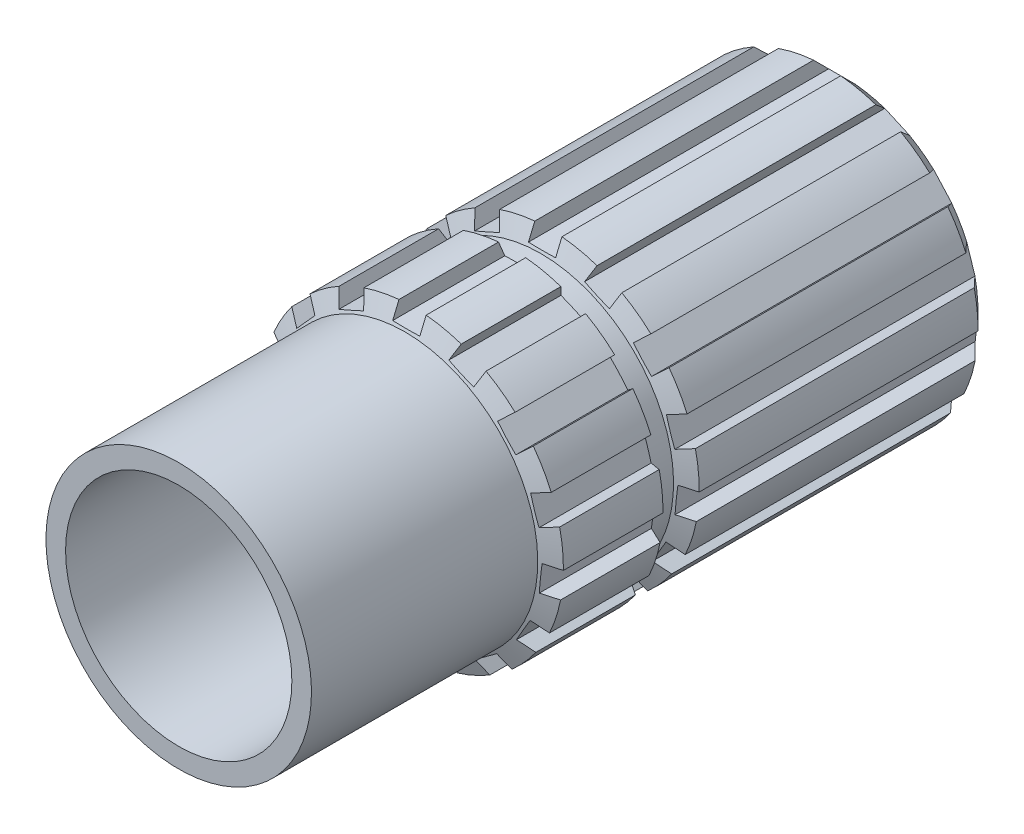
SolidWorks part; units mm, degrees
ref_plane "Front Plane" through (0, 0, 0) normal (0, 0, 1) x (1, 0, 0)
ref_plane "Top Plane" through (0, 0, 0) normal (0, 1, 0) x (1, 0, 0)
ref_plane "Right Plane" through (0, 0, 0) normal (1, 0, 0) x (0, 0, -1)
sketch "Sketch2" plane through (0, 0, 0) normal (1, 0, 0) x (0, 0, -1)
  line L0 (0, 0) -> (-103.5514, 0) construction
  line L1 (-27.9286, 9.525) -> (27.9286, 9.525)
  line L2 (27.9286, 9.525) -> (27.9286, 12.7)
  line L3 (-27.9286, 11.176) -> (-8.8786, 11.176)
  line L4 (-27.9286, 11.176) -> (-27.9286, 9.525)
  line L5 (-8.8786, 11.176) -> (-8.2436, 12.7)
  line L6 (-8.2436, 12.7) -> (0.1384, 12.7)
  line L7 (0.1384, 12.7) -> (0.7734, 11.176)
  line L8 (0.7734, 11.176) -> (2.5514, 11.176)
  line L9 (2.5514, 11.176) -> (3.1864, 12.7)
  line L10 (3.1864, 12.7) -> (27.9286, 12.7)
  point P5 (0, 9.525)
  dimension "D1" = 9.525
  dimension "D2" = 12.7
  dimension "D3" = 55.8571
  dimension "D4" = 1.651
  dimension "D5" = 0.635
  dimension "D6" = 0.635
  dimension "D7" = 0.635
  dimension "D8" = 19.05
  dimension "D9" = 1.778
  dimension "D10" = 9.652
revolve "Revolve1" add sketch "Sketch2" angle 360 about L0
chamfer "Chamfer1" distance 1.27 angle 45 1 edges at (0, 12.7, -27.9286)
sketch "Sketch3" plane through (0, 0, -27.9286) normal (0, 0, -1) x (-1, 0, 0)
  line L0 (0, 0.1797) -> (0, 13.5361) construction
  line L1 (-1.143, 11.3785) -> (1.143, 11.3785)
  line L2 (1.143, 11.3785) -> (1.143, 12.6485)
  line L3 (-1.143, 11.3785) -> (-1.143, 12.6485)
  line L4 (3.5839, 10.8596) -> (4.1004, 12.0198)
  line L5 (3.5839, 10.8596) -> (5.6722, 9.9298)
  line L6 (5.6722, 9.9298) -> (6.1888, 11.09)
  line L7 (7.691, 8.4631) -> (8.6348, 9.3129)
  line L8 (7.691, 8.4631) -> (9.2207, 6.7643)
  line L9 (9.2207, 6.7643) -> (10.1645, 7.6141)
  line L10 (10.4684, 4.6032) -> (11.6762, 4.9956)
  line L11 (10.4684, 4.6032) -> (11.1748, 2.4291)
  line L12 (11.1748, 2.4291) -> (12.3826, 2.8215)
  line L13 (11.4356, -0.0526) -> (12.6986, -0.1854)
  line L14 (11.4356, -0.0526) -> (11.1967, -2.3261)
  line L15 (11.1967, -2.3261) -> (12.4597, -2.4589)
  line L16 (10.4255, -4.6994) -> (11.5254, -5.3344)
  line L17 (10.4255, -4.6994) -> (9.2825, -6.6791)
  line L18 (9.2825, -6.6791) -> (10.3824, -7.3141)
  line L19 (7.6128, -8.5335) -> (8.3593, -9.561)
  line L20 (7.6128, -8.5335) -> (5.7634, -9.8772)
  line L21 (5.7634, -9.8772) -> (6.5099, -10.9047)
  line L22 (3.4837, -10.8922) -> (3.7478, -12.1344)
  line L23 (3.4837, -10.8922) -> (1.2477, -11.3675)
  line L24 (1.2477, -11.3675) -> (1.5117, -12.6097)
  line L25 (-1.2477, -11.3675) -> (-1.5117, -12.6097)
  line L26 (-1.2477, -11.3675) -> (-3.4837, -10.8922)
  line L27 (-3.4837, -10.8922) -> (-3.7478, -12.1344)
  line L28 (-5.7634, -9.8772) -> (-6.5099, -10.9047)
  line L29 (-5.7634, -9.8772) -> (-7.6128, -8.5335)
  line L30 (-7.6128, -8.5335) -> (-8.3593, -9.561)
  line L31 (-9.2825, -6.6791) -> (-10.3824, -7.3141)
  line L32 (-9.2825, -6.6791) -> (-10.4255, -4.6994)
  line L33 (-10.4255, -4.6994) -> (-11.5254, -5.3344)
  line L34 (-11.1967, -2.3261) -> (-12.4597, -2.4589)
  line L35 (-11.1967, -2.3261) -> (-11.4356, -0.0526)
  line L36 (-11.4356, -0.0526) -> (-12.6986, -0.1854)
  line L37 (-11.1748, 2.4291) -> (-12.3826, 2.8215)
  line L38 (-11.1748, 2.4291) -> (-10.4684, 4.6032)
  line L39 (-10.4684, 4.6032) -> (-11.6762, 4.9956)
  line L40 (-9.2207, 6.7643) -> (-10.1645, 7.6141)
  line L41 (-9.2207, 6.7643) -> (-7.691, 8.4631)
  line L42 (-7.691, 8.4631) -> (-8.6348, 9.3129)
  line L43 (-5.6722, 9.9298) -> (-6.1888, 11.09)
  line L44 (-5.6722, 9.9298) -> (-3.5839, 10.8596)
  line L45 (-3.5839, 10.8596) -> (-4.1004, 12.0198)
  circle A0 centre (0, 0) radius 12.7 construction
  arc A1 (-10.1645, 7.6141) -> (-11.6762, 4.9956) centre (0, 0) ccw
  arc A2 (-6.1888, 11.09) -> (-8.6348, 9.3129) centre (0, 0) ccw
  arc A3 (-1.143, 12.6485) -> (-4.1004, 12.0198) centre (0, 0) ccw
  arc A4 (4.1004, 12.0198) -> (1.143, 12.6485) centre (0, 0) ccw
  arc A5 (8.6348, 9.3129) -> (6.1888, 11.09) centre (0, 0) ccw
  arc A6 (11.6762, 4.9956) -> (10.1645, 7.6141) centre (0, 0) ccw
  arc A7 (12.6986, -0.1854) -> (12.3826, 2.8215) centre (0, 0) ccw
  arc A8 (11.5254, -5.3344) -> (12.4597, -2.4589) centre (0, 0) ccw
  arc A9 (8.3593, -9.561) -> (10.3824, -7.3141) centre (0, 0) ccw
  arc A10 (3.7478, -12.1344) -> (6.5099, -10.9047) centre (0, 0) ccw
  arc A11 (-1.5117, -12.6097) -> (1.5117, -12.6097) centre (0, 0) ccw
  arc A12 (-6.5099, -10.9047) -> (-3.7478, -12.1344) centre (0, 0) ccw
  arc A13 (-10.3824, -7.3141) -> (-8.3593, -9.561) centre (0, 0) ccw
  arc A14 (-12.4597, -2.4589) -> (-11.5254, -5.3344) centre (0, 0) ccw
  arc A15 (-12.3826, 2.8215) -> (-12.6986, -0.1854) centre (0, 0) ccw
  point P10 (0, 11.3785)
  dimension "D1" = 1.143
  dimension "D2" = 1.27
  dimension "D3" = 15
extrude "Cut-Extrude3" cut sketch "Sketch3" against normal through all flip side to cut
